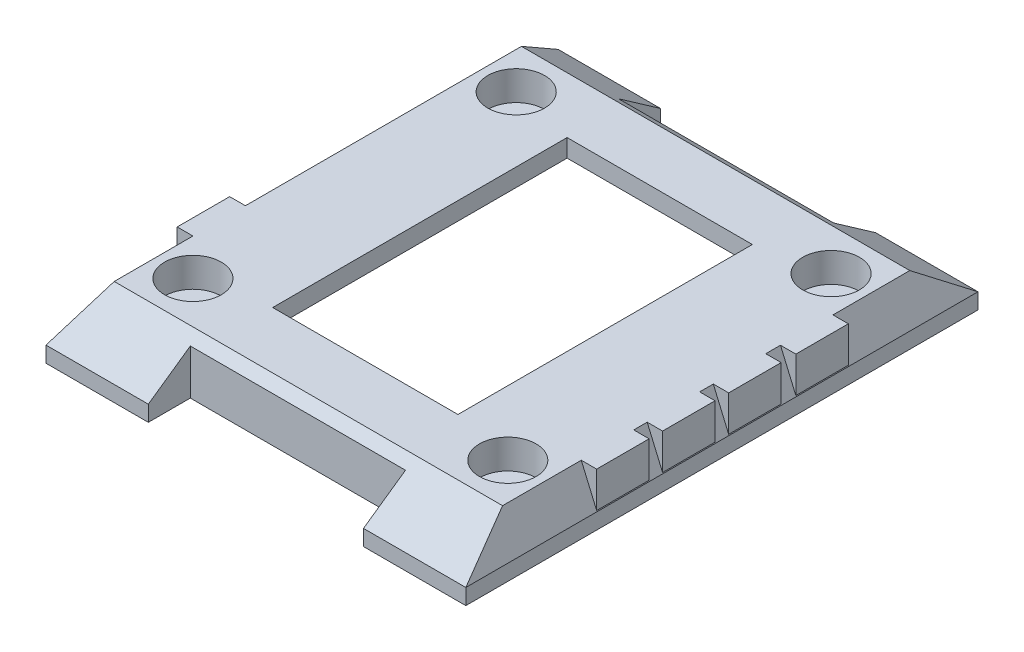
SolidWorks part; units mm, degrees
ref_plane "Front Plane" through (0, 0, 0) normal (0, 0, 1) x (1, 0, 0)
ref_plane "Top Plane" through (0, 0, 0) normal (0, 1, 0) x (1, 0, 0)
ref_plane "Right Plane" through (0, 0, 0) normal (1, 0, 0) x (0, 0, -1)
sketch "Sketch1" plane through (0, 0, 0) normal (0, 1, 0) x (1, 0, 0)
  line L1 (-35.1449, 25.1812) -> (4.8551, 25.1812)
  line L2 (-35.1449, 25.1812) -> (-35.1449, -23.6188)
  line L3 (-35.1449, -23.6188) -> (4.8551, -23.6188)
  line L4 (4.8551, 25.1812) -> (4.8551, -23.6188)
  dimension "D1" = 48.8
  dimension "D2" = 40
extrude "Boss-Extrude1" add sketch "Sketch1" along normal blind 5
sketch "Sketch2" plane through (0, 5, 0) normal (0, 1, 0) x (1, 0, 0)
  line L0 (-15.1449, -23.6188) -> (-15.1449, 25.1812) construction
  line L1 (-35.1449, -23.6188) -> (4.8551, -23.6188) construction
  line L2 (4.8551, 25.1812) -> (-35.1449, 25.1812) construction
  line L4 (-4.8949, -27.6188) -> (-25.3949, -27.6188)
  line L5 (-4.8949, -27.6188) -> (-4.8949, -19.6188)
  line L6 (-4.8949, -19.6188) -> (-25.3949, -19.6188)
  line L7 (-25.3949, -27.6188) -> (-25.3949, -19.6188)
  line L8 (-4.8949, -27.6188) -> (-25.3949, -19.6188) construction
  line L9 (-4.8949, -19.6188) -> (-25.3949, -27.6188) construction
  line L10 (-4.8949, 29.1812) -> (-25.3949, 29.1812)
  line L11 (-4.8949, 29.1812) -> (-4.8949, 21.1812)
  line L12 (-4.8949, 21.1812) -> (-25.3949, 21.1812)
  line L13 (-25.3949, 29.1812) -> (-25.3949, 21.1812)
  line L14 (-4.8949, 29.1812) -> (-25.3949, 21.1812) construction
  line L15 (-4.8949, 21.1812) -> (-25.3949, 29.1812) construction
  dimension "D1" = 20.5
  dimension "D2" = 8
extrude "Cut-Extrude1" cut sketch "Sketch2" against normal through all
sketch "Sketch3" plane through (0, 5, 0) normal (0, 1, 0) x (1, 0, 0)
  line L0 (-15.1449, 21.1812) -> (-15.1449, -19.6188) construction
  line L1 (-25.3949, 21.1812) -> (-4.8949, 21.1812) construction
  line L2 (-4.8949, -19.6188) -> (-25.3949, -19.6188) construction
  line L3 (-35.1449, 0.7812) -> (4.8551, 0.7812) construction
  line L4 (-35.1449, 25.1812) -> (-35.1449, -23.6188) construction
  line L5 (4.8551, -23.6188) -> (4.8551, 25.1812) construction
  line L7 (-0.1449, -14.6188) -> (-30.1449, -14.6188) construction
  line L8 (-0.1449, -14.6188) -> (-0.1449, 16.1812) construction
  line L9 (-0.1449, 16.1812) -> (-30.1449, 16.1812) construction
  line L10 (-30.1449, -14.6188) -> (-30.1449, 16.1812) construction
  line L11 (-0.1449, -14.6188) -> (-30.1449, 16.1812) construction
  line L12 (-0.1449, 16.1812) -> (-30.1449, -14.6188) construction
  circle A0 centre (-30.1449, 16.1812) radius 2.7
  circle A1 centre (-0.1449, 16.1812) radius 2.7
  circle A2 centre (-30.1449, -14.6188) radius 2.7
  circle A3 centre (-0.1449, -14.6188) radius 2.7
  point P12 (-15.1449, 0.7812)
  dimension "D3" = 5.4
  dimension "D1" = 30
  dimension "D2" = 30.8
extrude "Cut-Extrude2" cut sketch "Sketch3" against normal blind 2.8
sketch "Sketch5" plane through (0, 5, 0) normal (0, 1, 0) x (1, 0, 0)
  circle A0 centre (-30.1449, -14.6188) radius 1
  circle A1 centre (-0.1449, -14.6188) radius 1
  circle A2 centre (-0.1449, 16.1812) radius 1
  circle A3 centre (-30.1449, 16.1812) radius 1
  dimension "D1" = 2
extrude "Cut-Extrude3" cut sketch "Sketch5" against normal through all
sketch "Sketch6" plane through (4.8551, 0, 0) normal (1, 0, 0) x (0, 0, -1)
  line L0 (0.7812, 0) -> (0.7812, 5) construction
  line L1 (-23.6188, 0) -> (25.1812, 0) construction
  line L2 (-23.6188, 5) -> (25.1812, 5) construction
  line L3 (-18.6188, 5) -> (-23.6188, 1.5)
  line L4 (25.1812, 1.5) -> (25.1812, 0)
  line L5 (20.1812, 5) -> (25.1812, 1.5)
  line L6 (-23.6188, 1.5) -> (-23.6188, 0)
  line L7 (-23.6188, 0) -> (25.1812, 0)
  line L9 (20.1812, 5) -> (-18.6188, 5)
  dimension "D1" = 5
  dimension "D3" = 1.5
extrude "Cut-Extrude4" cut sketch "Sketch6" against normal through all flip side to cut
sketch "Sketch7" plane through (0, 0, 23.6188) normal (0, 0, 1) x (1, 0, 0)
  line L0 (4.8551, 1.5) -> (3.3551, 5)
  line L1 (4.8551, 1.5) -> (4.8551, 0)
  line L2 (-35.1449, 5) -> (4.8551, 5) construction
  line L3 (-35.1449, 1.5) -> (4.8551, 1.5) construction
  line L4 (-15.1449, 1.5) -> (-15.1449, 4.6859) construction
  line L5 (-35.1449, 1.5) -> (-35.1449, 0)
  line L6 (-35.1449, 1.5) -> (-33.6449, 5)
  line L7 (-33.6449, 5) -> (3.3551, 5)
  line L8 (4.8551, 0) -> (-35.1449, 0)
  dimension "D1" = 1.5
extrude "Cut-Extrude5" cut sketch "Sketch7" against normal through all flip side to cut
sketch "Sketch8" plane through (0, 5, 0) normal (0, 1, 0) x (1, 0, 0)
  line L1 (-6.2949, 14.8312) -> (-23.9449, 14.8312)
  line L2 (-6.2949, 14.8312) -> (-6.2949, -13.2188)
  line L3 (-6.2949, -13.2188) -> (-23.9449, -13.2188)
  line L4 (-23.9449, 14.8312) -> (-23.9449, -13.2188)
  line L5 (-6.2949, 14.8312) -> (-23.9449, -13.2188) construction
  line L6 (-6.2949, -13.2188) -> (-23.9449, 14.8312) construction
  circle A0 centre (-0.1449, -14.6188) radius 1 construction
  circle A1 centre (-30.1449, -14.6188) radius 1 construction
  point P0 (-15.1199, 0.8062)
  dimension "D5" = 6.2
  dimension "D1" = 17.65
  dimension "D2" = 28.05
  dimension "D3" = 1.4
extrude "Cut-Extrude6" cut sketch "Sketch8" against normal through all
sketch "Sketch9" plane through (0, 5, 0) normal (0, 1, 0) x (1, 0, 0)
  line L1 (3.3551, 20.1812) -> (3.3551, -18.6188) construction
  line L2 (1.8898, 7.8612) -> (4.8203, 7.8612)
  line L3 (1.8898, 7.8612) -> (1.8898, 12.8612)
  line L4 (1.8898, 12.8612) -> (4.8203, 12.8612)
  line L5 (4.8203, 7.8612) -> (4.8203, 12.8612)
  line L6 (1.8898, 7.8612) -> (4.8203, 12.8612) construction
  line L7 (1.8898, 12.8612) -> (4.8203, 7.8612) construction
  line L8 (-4.8949, -23.6188) -> (4.8551, -23.6188) construction
  line L9 (-33.6449, 20.1812) -> (-33.6449, -18.6188) construction
  line L10 (4.8203, 6.4612) -> (1.8898, 6.4612)
  line L11 (4.8203, 6.4612) -> (4.8203, 1.4612)
  line L12 (4.8203, 1.4612) -> (1.8898, 1.4612)
  line L13 (1.8898, 6.4612) -> (1.8898, 1.4612)
  line L14 (4.8203, 6.4612) -> (1.8898, 1.4612) construction
  line L15 (4.8203, 1.4612) -> (1.8898, 6.4612) construction
  line L16 (4.8203, 0.1612) -> (1.8898, 0.1612)
  line L18 (4.8203, 0.1612) -> (4.8203, -4.8388)
  line L19 (4.8203, -4.8388) -> (1.8898, -4.8388)
  line L20 (1.8898, 0.1612) -> (1.8898, -4.8388)
  line L21 (4.8203, 0.1612) -> (1.8898, -4.8388) construction
  line L23 (4.8203, -4.8388) -> (1.8898, 0.1612) construction
  line L24 (4.8203, -11.1188) -> (1.8898, -11.1188)
  line L25 (4.8203, -11.1188) -> (4.8203, -6.1188)
  line L26 (4.8203, -6.1188) -> (1.8898, -6.1188)
  line L27 (1.8898, -11.1188) -> (1.8898, -6.1188)
  line L28 (4.8203, -11.1188) -> (1.8898, -6.1188) construction
  line L29 (4.8203, -6.1188) -> (1.8898, -11.1188) construction
  line L30 (-32.1449, -11.1188) -> (-35.1449, -11.1188)
  line L31 (-32.1449, -11.1188) -> (-32.1449, -6.1188)
  line L32 (-32.1449, -6.1188) -> (-35.1449, -6.1188)
  line L33 (-35.1449, -11.1188) -> (-35.1449, -6.1188)
  line L34 (-32.1449, -11.1188) -> (-35.1449, -6.1188) construction
  line L35 (-32.1449, -6.1188) -> (-35.1449, -11.1188) construction
  line L36 (-35.1449, -23.6188) -> (-25.3949, -23.6188) construction
  line L37 (-35.1449, 25.1812) -> (-35.1449, -23.6188) construction
  point P0 (3.3551, 10.3612)
  point P9 (3.3551, 3.9612)
  point P14 (-0.0199, -23.6188)
  point P15 (3.3551, -2.3388)
  point P20 (3.3551, -8.6188)
  point P25 (-0.0199, -23.6188)
  point P26 (-33.6449, -8.6188)
  dimension "D1" = 33.98
  dimension "D2" = 5
  dimension "D3" = 27.58
  dimension "D4" = 21.28
  dimension "D5" = 15
  dimension "D6" = 15
  dimension "D7" = 5
extrude "Boss-Extrude2" add sketch "Sketch9" against normal through all
sketch "Sketch10" plane through (0, 0, 0) normal (0, -1, 0) x (1, 0, 0)
  line L0 (4.8551, -25.1812) -> (-35.1449, 23.6188) construction
  line L1 (4.8551, 23.6188) -> (-35.1449, -25.1812) construction
  line L3 (-33.0449, 18.2188) -> (2.7551, 18.2188)
  line L4 (-33.0449, 18.2188) -> (-33.0449, -19.7812)
  line L5 (-33.0449, -19.7812) -> (2.7551, -19.7812)
  line L6 (2.7551, 18.2188) -> (2.7551, -19.7812)
  line L7 (-33.0449, 18.2188) -> (2.7551, -19.7812) construction
  line L8 (-33.0449, -19.7812) -> (2.7551, 18.2188) construction
  point P8 (-15.1449, -0.7812)
  dimension "D1" = 38
  dimension "D2" = 35.8
extrude "Cut-Extrude7" cut sketch "Sketch10" against normal blind 0.8
sketch "Sketch11" plane through (0, 0, 0) normal (0, -1, 0) x (1, 0, 0)
  line L1 (-33.0449, 18.2188) -> (2.7551, 18.2188) construction
  line L2 (-33.0449, 18.2188) -> (-33.0449, -19.7812) construction
  line L3 (-33.0449, -19.7812) -> (2.7551, -19.7812) construction
  line L4 (2.7551, 18.2188) -> (2.7551, -19.7812) construction
  line L5 (-33.0449, 18.2188) -> (2.7551, -19.7812) construction
  line L6 (-33.0449, -19.7812) -> (2.7551, 18.2188) construction
  line L7 (-33.1449, 11.2188) -> (2.8551, 11.2188)
  line L8 (-33.1449, 11.2188) -> (-33.1449, -12.7812)
  line L9 (-33.1449, -12.7812) -> (2.8551, -12.7812)
  line L10 (2.8551, 11.2188) -> (2.8551, -12.7812)
  line L11 (-33.1449, 11.2188) -> (2.8551, -12.7812) construction
  line L12 (-33.1449, -12.7812) -> (2.8551, 11.2188) construction
  point P0 (-15.1449, -0.7812)
  point P5 (-15.1449, -0.7812)
  dimension "D1" = 36
  dimension "D2" = 24
extrude "Cut-Extrude8" cut sketch "Sketch11" against normal blind 2.8
sketch "Sketch12" plane through (0, 0, 0) normal (0, -1, 0) x (1, 0, 0)
  line L0 (4.8551, 23.6188) -> (4.8551, -25.1812) construction
  line L1 (-7.1449, -14.2812) -> (-3.1449, -14.2812)
  line L2 (-7.1449, -14.2812) -> (-7.1449, 12.4188)
  line L3 (-7.1449, 12.4188) -> (-3.1449, 12.4188)
  line L4 (-3.1449, -14.2812) -> (-3.1449, 12.4188)
  line L5 (-7.1449, -14.2812) -> (-3.1449, 12.4188) construction
  line L6 (-7.1449, 12.4188) -> (-3.1449, -14.2812) construction
  line L7 (-4.8949, 23.6188) -> (4.8551, 23.6188) construction
  point P0 (-5.1449, -0.9312)
  dimension "D1" = 4
  dimension "D2" = 8
  dimension "D3" = 11.2
  dimension "D4" = 26.7
extrude "Cut-Extrude9" cut sketch "Sketch12" against normal blind 3.3
sketch "Sketch13" plane through (0, 0, 0) normal (0, -1, 0) x (1, 0, 0)
  line L1 (-35.1449, 23.6188) -> (4.8551, 23.6188)
  line L2 (-35.1449, 23.6188) -> (-35.1449, -25.1812)
  line L3 (-35.1449, -25.1812) -> (4.8551, -25.1812)
  line L4 (4.8551, 23.6188) -> (4.8551, -25.1812)
  line L5 (-35.1449, 23.6188) -> (4.8551, -25.1812) construction
  line L6 (-35.1449, -25.1812) -> (4.8551, 23.6188) construction
  line L9 (2.8551, -13.1812) -> (-3.1449, -13.1812)
  line L10 (-3.1449, -19.7761) -> (-3.1449, -13.1812)
  line L13 (-33.1449, -13.1812) -> (-27.1449, -13.1812)
  line L14 (-27.1449, -19.7812) -> (-27.1449, -13.1812)
  line L17 (-33.1449, 11.6188) -> (-27.1449, 11.6188)
  line L18 (-27.1449, 18.2188) -> (-27.1449, 11.6188)
  line L21 (2.8551, 11.6188) -> (-3.1449, 11.6188)
  line L22 (-3.1449, 18.2188) -> (-3.1449, 11.6188)
  line L23 (-3.1449, 18.2188) -> (-27.1449, 18.2188)
  line L25 (2.7551, 18.2188) -> (-33.0449, 18.2188) construction
  line L26 (-3.1449, -19.7761) -> (-27.1449, -19.7812)
  line L27 (-33.0449, -19.7812) -> (2.7551, -19.7812) construction
  line L28 (2.8551, 11.6188) -> (2.8551, -13.1812)
  line L29 (2.8551, -12.7812) -> (2.8551, 11.2188) construction
  line L30 (-33.1449, 11.6188) -> (-33.1449, -13.1812)
  line L31 (-33.1449, 11.2188) -> (-33.1449, -12.7812) construction
  circle A0 centre (-0.1449, 14.6188) radius 1 construction
  circle A1 centre (-30.1449, 14.6188) radius 1 construction
  circle A2 centre (-30.1449, -16.1812) radius 1 construction
  circle A3 centre (-0.1449, -16.1812) radius 1 construction
  circle A4 centre (-0.1449, -16.1812) radius 1 construction
  point P0 (-15.1449, -0.7812)
  dimension "D1" = 3
  dimension "D2" = 3
  dimension "D3" = 3
  dimension "D4" = 3
  dimension "D5" = 3
  dimension "D6" = 3
  dimension "D8" = 3
  dimension "D7" = 3
extrude "Cut-Extrude10" cut sketch "Sketch13" against normal blind 3.3 flip side to cut
sketch "Sketch14" plane through (0, 0, 0) normal (0, -1, 0) x (1, 0, 0)
  line L0 (-30.6449, -16.4143) -> (-30.6449, 10.6613) construction
  line L2 (-30.6449, -12.9812) -> (-34.4449, -12.9812)
  line L3 (-30.6449, -12.9812) -> (-30.6449, -8.4812)
  line L4 (-30.6449, -8.4812) -> (-34.4449, -8.4812)
  line L5 (-34.4449, -12.9812) -> (-34.4449, -8.4812)
  circle A3 centre (-30.1449, -16.1812) radius 1 construction
  dimension "D1" = 0.5
  dimension "D2" = 3.8
  dimension "D3" = 4.5
  dimension "D4" = 3.2
revolve "Cut-Revolve1" cut sketch "Sketch14" angle 360 about L0
fillet "Fillet1" radius 2 4 edges at (-27.1449, 2.05, 11.6188) (-3.1449, 2.05, 11.6188) (-3.1449, 2.05, -13.1812) (-27.1449, 2.05, -13.1812)
